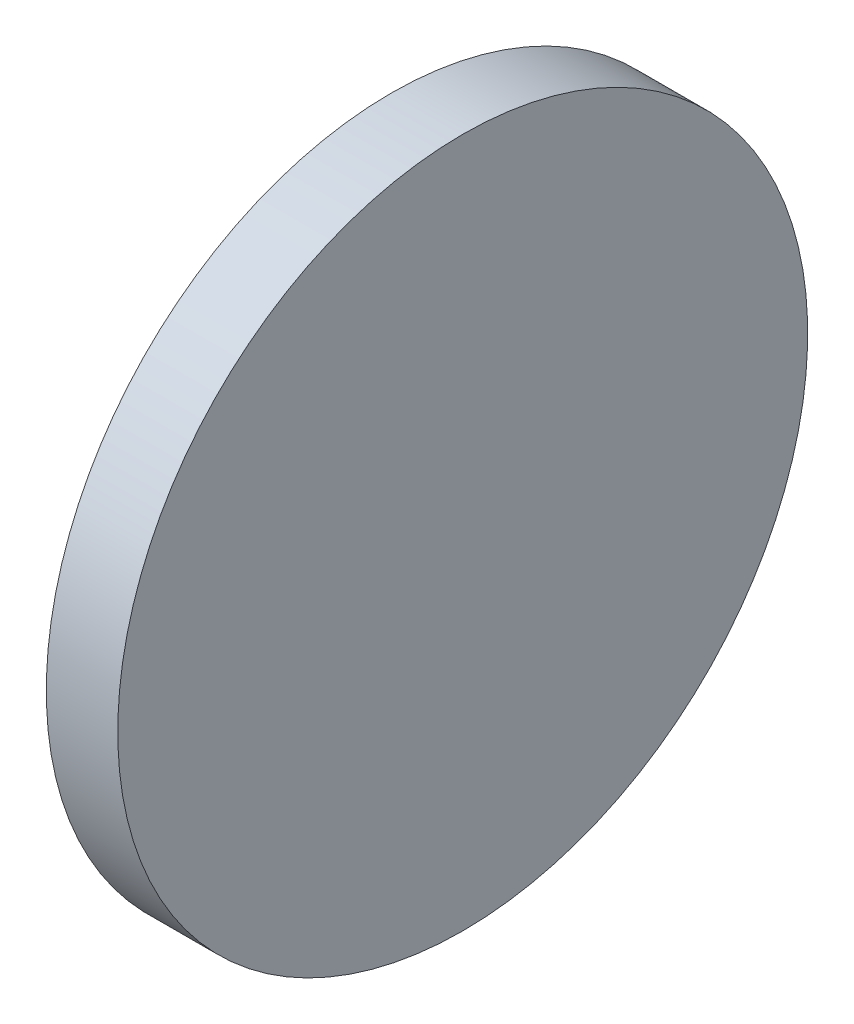
SolidWorks part; units mm, degrees
ref_plane "前视基准面" through (0, 0, 0) normal (0, 0, 1) x (1, 0, 0)
ref_plane "上视基准面" through (0, 0, 0) normal (0, 1, 0) x (1, 0, 0)
ref_plane "右视基准面" through (0, 0, 0) normal (1, 0, 0) x (0, 0, -1)
sketch "草图1" plane through (0, 0, 0) normal (0, 0, 1) x (1, 0, 0)
  line L0 (115.9445, 65.2168) -> (135.9482, 65.2168) construction
  line L1 (122.7876, 77.7168) -> (125.3765, 77.7168)
  line L2 (122.6114, 65.2168) -> (125.3114, 65.2168)
  arc A0 (122.7876, 77.7168) -> (122.6114, 65.2168) centre (566.1114, 65.2168) ccw
  arc A1 (125.3765, 77.7168) -> (125.3114, 65.2168) centre (1325.3114, 65.2168) ccw
revolve "旋转1" add sketch "草图1" angle 360 about L0
